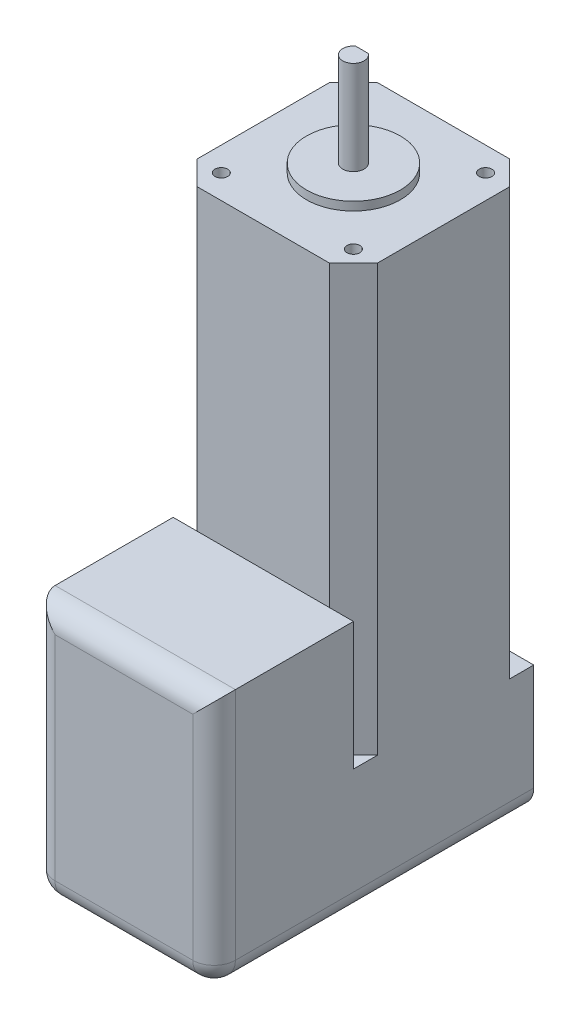
SolidWorks part; units mm, degrees
ref_plane "Front Plane" through (0, 0, 0) normal (0, 0, 1) x (1, 0, 0)
ref_plane "Top Plane" through (0, 0, 0) normal (0, 1, 0) x (1, 0, 0)
ref_plane "Right Plane" through (0, 0, 0) normal (1, 0, 0) x (0, 0, -1)
sketch "Sketch1" plane through (0, 0, 0) normal (0, 1, 0) x (1, 0, 0)
  line L0 (0, 36.65) -> (5.65, 36.65) construction
  line L1 (5.65, 0) -> (36.65, 0)
  line L2 (0, 5.65) -> (0, 36.65)
  line L3 (5.65, 42.3) -> (36.65, 42.3)
  line L4 (42.3, 5.65) -> (42.3, 36.65)
  line L5 (5.65, 36.65) -> (36.65, 36.65) construction
  line L6 (36.65, 36.65) -> (42.3, 36.65) construction
  line L7 (36.65, 42.3) -> (36.65, 36.65) construction
  line L8 (36.65, 36.65) -> (36.65, 5.65) construction
  line L9 (36.65, 5.65) -> (36.65, 0) construction
  line L10 (5.65, 42.3) -> (5.65, 36.65) construction
  line L11 (5.65, 36.65) -> (5.65, 5.65) construction
  line L12 (5.65, 5.65) -> (5.65, 0) construction
  line L13 (42.3, 5.65) -> (36.65, 5.65) construction
  line L14 (36.65, 5.65) -> (5.65, 5.65) construction
  line L15 (5.65, 5.65) -> (0, 5.65) construction
  line L16 (5.65, 42.3) -> (0, 36.65)
  line L17 (36.65, 42.3) -> (42.3, 36.65)
  line L18 (42.3, 5.65) -> (36.65, 0)
  line L19 (5.65, 0) -> (0, 5.65)
  line L20 (0, 0) -> (0, 5.65) construction
  line L21 (0, 0) -> (5.65, 0) construction
  circle A0 centre (5.65, 5.65) radius 1.5
  circle A1 centre (36.65, 5.65) radius 1.5
  circle A2 centre (36.65, 36.65) radius 1.5
  circle A3 centre (5.65, 36.65) radius 1.5
  dimension "D5" = 3
  dimension "D1" = 42.3
  dimension "D2" = 42.3
  dimension "D3" = 31
  dimension "D4" = 31
extrude "Boss-Extrude1" add sketch "Sketch1" along normal blind 15
sketch "Sketch2" plane through (0, 0, 0) normal (0, -1, 0) x (1, 0, 0)
  line L0 (5.65, 0) -> (0, -5.65)
  line L1 (0, -5.65) -> (0, -36.65)
  line L2 (0, -36.65) -> (5.65, -42.3)
  line L3 (5.65, -42.3) -> (36.65, -42.3)
  line L4 (36.65, -42.3) -> (42.3, -36.65)
  line L5 (42.3, -36.65) -> (42.3, -5.65)
  line L6 (42.3, -5.65) -> (36.65, 0)
  line L7 (36.65, 0) -> (5.65, 0)
extrude "Boss-Extrude2" add sketch "Sketch2" along normal blind 85
sketch "Sketch3" plane through (0, 15, 0) normal (0, 1, 0) x (1, 0, 0)
  line L0 (21.15, 42.3) -> (21.15, 0) construction
  line L1 (36.65, 42.3) -> (5.65, 42.3) construction
  line L2 (5.65, 0) -> (36.65, 0) construction
  circle A0 centre (21.15, 21.15) radius 11
  dimension "D1" = 22
extrude "Boss-Extrude3" add sketch "Sketch3" along normal blind 2
sketch "Sketch4" plane through (0, 17, 0) normal (0, 1, 0) x (1, 0, 0)
  line L0 (21.15, 32.15) -> (21.15, 10.15) construction
  circle A0 centre (21.15, 21.15) radius 11 construction
  circle A1 centre (21.15, 21.15) radius 11 construction
  circle A2 centre (21.15, 21.15) radius 2.5
  dimension "D1" = 5
extrude "Boss-Extrude4" add sketch "Sketch4" along normal blind 22
sketch "Sketch5" plane through (0, 39, 0) normal (0, 1, 0) x (1, 0, 0)
  line L0 (21.15, 18.65) -> (21.15, 23.15) construction
  line L1 (19.65, 23.15) -> (22.65, 23.15)
  circle A0 centre (21.15, 21.15) radius 2.5 construction
  circle A1 centre (21.15, 21.15) radius 2.5 construction
  arc A2 (19.65, 23.15) -> (22.65, 23.15) centre (21.15, 21.15) cw
  point P10 (21.15, 23.15)
  dimension "D1" = 4.5
extrude "Cut-Extrude1" cut sketch "Sketch5" against normal blind 15
sketch "Sketch6" plane through (0, -85, 0) normal (0, -1, 0) x (1, 0, 0)
  line L0 (0, -5.65) -> (0, -36.65) construction
  line L1 (42.3, 32.7) -> (0, 32.7)
  line L2 (42.3, 32.7) -> (42.3, -42.3)
  line L3 (42.3, -42.3) -> (0, -42.3)
  line L4 (0, 32.7) -> (0, -42.3)
  line L5 (42.3, -36.65) -> (42.3, -5.65) construction
  line L6 (5.65, -42.3) -> (36.65, -42.3) construction
  dimension "D1" = 75
extrude "Boss-Extrude5" add sketch "Sketch6" along normal blind 30
sketch "Sketch7" plane through (0, -85, 0) normal (0, 1, 0) x (1, 0, 0)
  line L0 (42.3, 5.65) -> (42.3, -32.7) construction
  line L1 (0, -32.7) -> (42.3, -32.7)
  line L2 (0, -32.7) -> (0, 0)
  line L3 (0, 0) -> (42.3, 0)
  line L4 (42.3, -32.7) -> (42.3, 0)
extrude "Boss-Extrude6" add sketch "Sketch7" along normal blind 30
fillet "Fillet1" radius 5 6 edges at (21.15, -55, 32.7) (42.3, -85, 32.7) (42.3, -115, -4.8) (0, -115, -4.8) (0, -85, 32.7) (21.15, -115, 32.7)
